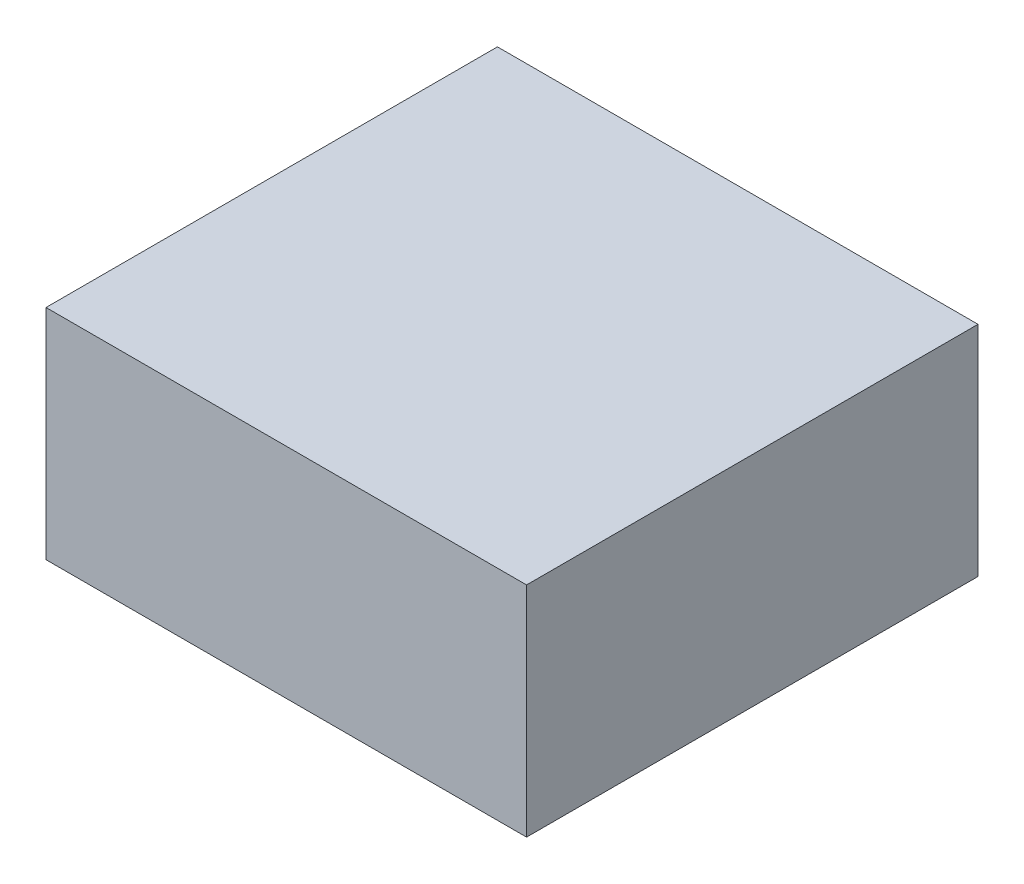
SolidWorks part; units mm, degrees
ref_plane "Plan de face" through (0, 0, 0) normal (0, 0, 1) x (1, 0, 0)
ref_plane "Plan de dessus" through (0, 0, 0) normal (0, 1, 0) x (1, 0, 0)
ref_plane "Plan de droite" through (0, 0, 0) normal (1, 0, 0) x (0, 0, -1)
sketch "Esquisse1" plane through (0, 0, 0) normal (0, 1, 0) x (1, 0, 0)
  line L1 (33, 31) -> (-33, 31)
  line L2 (33, 31) -> (33, -31)
  line L3 (33, -31) -> (-33, -31)
  line L4 (-33, 31) -> (-33, -31)
  line L5 (33, 31) -> (-33, -31) construction
  line L6 (33, -31) -> (-33, 31) construction
  point P0 (0, 0)
extrude "Boss.-Extru.1" add sketch "Esquisse1" along normal blind 30
